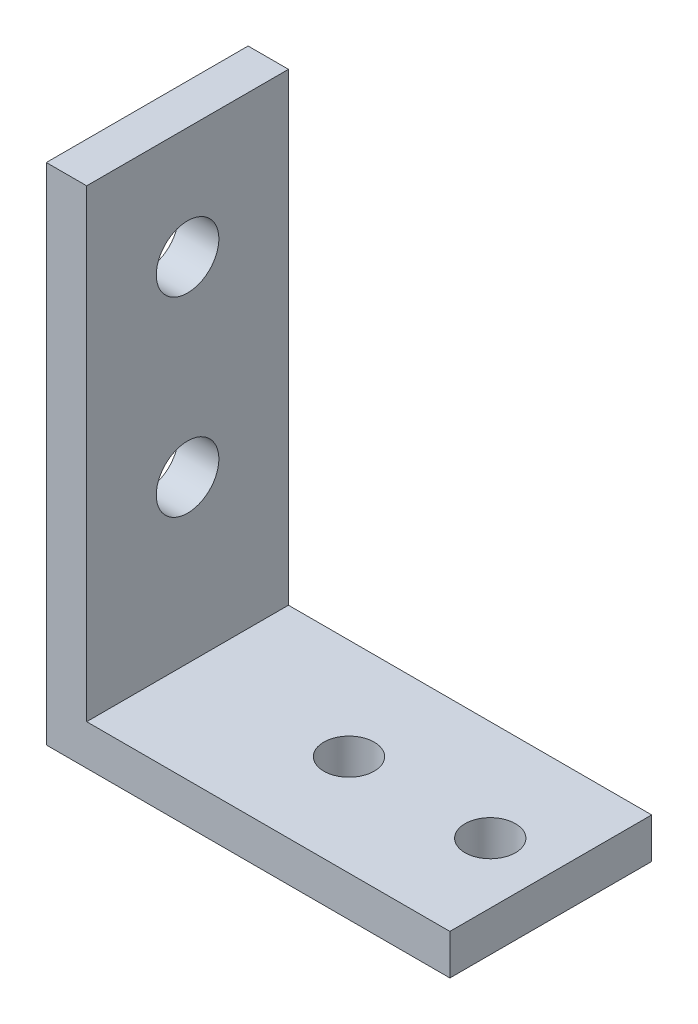
SolidWorks part; units mm, degrees
material "6063-T6"
ref_plane "Front Plane" through (0, 0, 0) normal (0, 0, 1) x (1, 0, 0)
ref_plane "Top Plane" through (0, 0, 0) normal (0, 1, 0) x (1, 0, 0)
ref_plane "Right Plane" through (0, 0, 0) normal (1, 0, 0) x (0, 0, -1)
sketch "Sketch1" plane through (0, 0, 0) normal (0, 0, 1) x (1, 0, 0)
  line L0 (0, 0) -> (0, 25)
  line L1 (0, 25) -> (2, 25)
  line L2 (2, 25) -> (2, 2)
  line L3 (2, 2) -> (20, 2)
  line L4 (20, 2) -> (20, 0)
  line L5 (20, 0) -> (0, 0)
  dimension "D1" = 2
  dimension "D2" = 25
  dimension "D3" = 20
extrude "Base" add sketch "Sketch1" along normal mid plane 10
hole_wizard "M3x0.5 MountHoles" positions "Sketch3" profile "Sketch4" tap size "M3x0.5" standard "ANSI Metric" end condition through all
sketch "Sketch3" plane through (0, 0, 0) normal (0, -1, 0) x (-1, 0, 0)
  line L1 (0, -5) -> (0, 5) construction
  point P0 (-10, 0)
  point P2 (-17, 0)
  dimension "D1" = 10
  dimension "D2" = 17
cosmetic thread "Hole Thread3"
cosmetic thread "Hole Thread4"
sketch "Sketch4" plane through (10, 0, 0) normal (1, 0, 0) x (0, 0, -1)
  line L0 (0, 0) -> (0, 25)
  line L1 (0, 25) -> (1.25, 25)
  line L2 (1.25, 25) -> (1.25, 0)
  line L5 (1.25, 0) -> (0, 0)
  line L11 (0, -6.35) -> (0, 107.95) construction
  dimension "Thru Tap Drill Dia." = 2.5
  dimension "Thru Tap Drill Depth" = 25
cosmetic thread "Cosmetic Thread2"
cosmetic thread "Cosmetic Thread3"
hole_wizard "Ø3.1 (3.1) LimitSwitchHoles" positions "3DSketch1" profile "Sketch5" hole size "Ø3.1" standard "ANSI Metric" end condition through all
sketch3d "3DSketch1"
  line L1 (0, 0, 5) -> (0, 0, -5) construction
  point P16 (0, 10, 0)
  point P18 (0, 19.45, 0)
  dimension "D1" = 10
  dimension "D2" = 19.45
sketch "Sketch5" plane through (0, 10, 0) normal (0, 1, 0) x (0, 0, 1)
  line L0 (0, 0) -> (0, 20)
  line L1 (0, 20) -> (1.55, 20)
  line L2 (1.55, 20) -> (1.55, 0)
  line L5 (1.55, 0) -> (0, 0)
  line L11 (0, -6.35) -> (0, 107.95) construction
  dimension "Thru Hole Dia." = 3.1
  dimension "Thru Hole Depth" = 20
